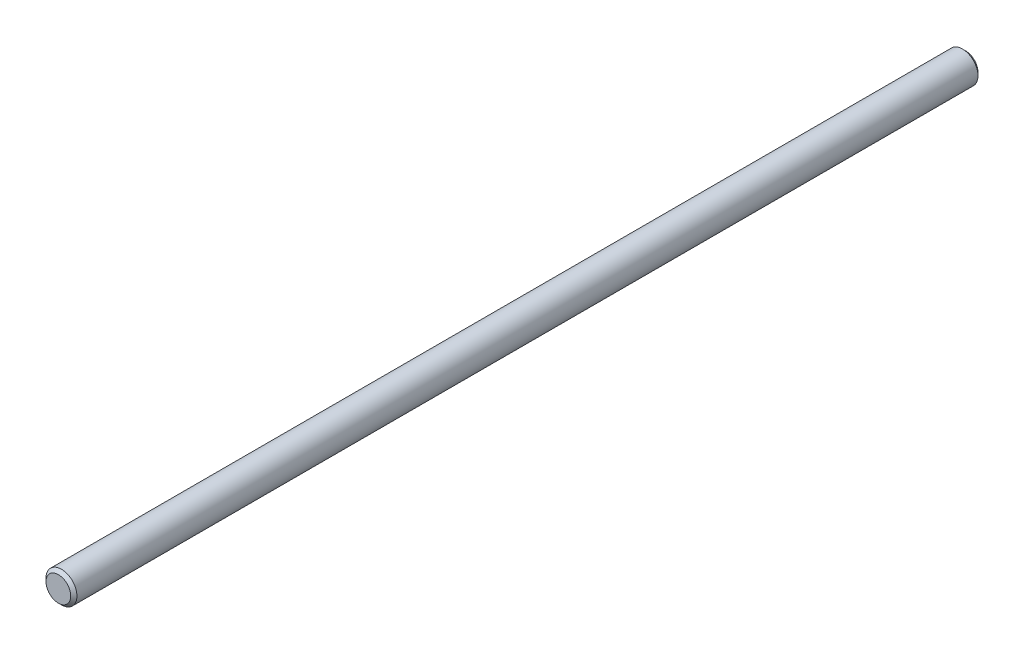
SolidWorks part; units mm, degrees
ref_plane "Front" through (0, 0, 0) normal (0, 0, 1) x (1, 0, 0)
ref_plane "Top" through (0, 0, 0) normal (0, 1, 0) x (1, 0, 0)
ref_plane "Right" through (0, 0, 0) normal (1, 0, 0) x (0, 0, -1)
sketch "Sketch1" plane through (0, 0, 0) normal (0, 0, 1) x (1, 0, 0)
  circle A0 centre (0, 0) radius 9.525
  dimension "D1" = 19.05
extrude "Extrude1" add sketch "Sketch1" along normal mid plane 558.8
chamfer "Chamfer1" distance 1.905 angle 45 2 edges at (9.525, 0, -279.4) (9.525, 0, 279.4)
equation "\"D1@Chamfer1\" = \"D1@Sketch1\" * .1"
